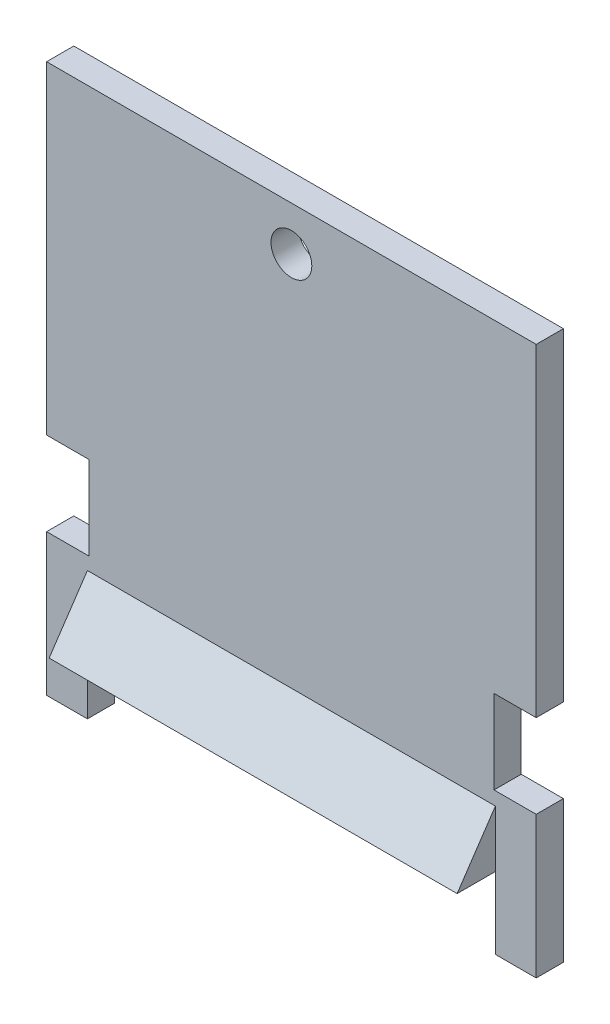
SolidWorks part; units mm, degrees
other "Camera1"
ref_plane "Front Plane" through (0, 0, 0) normal (0, 0, 1) x (1, 0, 0)
ref_plane "Top Plane" through (0, 0, 0) normal (0, 1, 0) x (1, 0, 0)
ref_plane "Right Plane" through (0, 0, 0) normal (1, 0, 0) x (0, 0, -1)
sketch "Sketch1" plane through (0, 0, 0) normal (1, 0, 0) x (0, 0, -1)
  line L0 (0, 0) -> (0, 40.35)
  line L1 (0, 40.35) -> (-2, 40.35)
  line L2 (-2, 40.35) -> (-2, 9.45)
  line L3 (-2, 9.45) -> (-6.5, 2.78)
  line L4 (-6.5, 2.78) -> (-2, 2.78)
  line L5 (-2, 2.78) -> (-2, 0)
  line L6 (-2, 0) -> (0, 0)
  dimension "D1" = 2
  dimension "D2" = 6.67
  dimension "D3" = 2.78
  dimension "D4" = 4.5
  dimension "D5" = 30.9
extrude "Boss-Extrude1" add sketch "Sketch1" along normal mid plane 36
sketch "Sketch2" plane through (0, 0, 0) normal (0, 0, -1) x (-1, 0, 0)
  line L0 (-18, 0) -> (18, 0) construction
  line L1 (-15, 0) -> (15, 0)
  line L2 (-15, 0) -> (-15, 2.78)
  line L3 (-15, 2.78) -> (15, 2.78)
  line L4 (15, 0) -> (15, 2.78)
  line L5 (-18, 2.78) -> (18, 2.78) construction
  line L6 (-18, 40.35) -> (18, 40.35) construction
  circle A0 centre (0, 37.1) radius 1.5
  point P6 (0, 2.78)
  dimension "D2" = 3
  dimension "D1" = 30
  dimension "D3" = 3.25
extrude "Cut-Extrude1" cut sketch "Sketch2" against normal through all
sketch "Sketch3" plane through (0, 0, 0) normal (0, 0, -1) x (-1, 0, 0)
  line L0 (-18, 0) -> (-18, 40.35) construction
  line L1 (-18, 16.575) -> (-14.9, 16.575)
  line L2 (-18, 16.575) -> (-18, 10.425)
  line L3 (-18, 10.425) -> (-14.9, 10.425)
  line L4 (-14.9, 16.575) -> (-14.9, 10.425)
  line L5 (18, 0) -> (18, 40.35) construction
  line L6 (18, 16.575) -> (14.9, 16.575)
  line L7 (18, 16.575) -> (18, 10.425)
  line L8 (18, 10.425) -> (14.9, 10.425)
  line L9 (14.9, 16.575) -> (14.9, 10.425)
  line L11 (-18, 0) -> (-15, 0) construction
  point P12 (-18, 13.5)
  dimension "D1" = 3.1
  dimension "D2" = 6.15
  dimension "D3" = 13.5
extrude "Cut-Extrude2" cut sketch "Sketch3" against normal through all
sketch "Sketch4" plane through (0, 0, 2) normal (0, 0, 1) x (1, 0, 0)
  line L0 (18, 2.78) -> (-18, 2.78) construction
  line L1 (-18, 10.425) -> (-15, 10.425)
  line L2 (-18, 10.425) -> (-18, 2.78)
  line L3 (-18, 2.78) -> (-15, 2.78)
  line L4 (-15, 10.425) -> (-15, 2.78)
  line L6 (18, 10.425) -> (15, 10.425)
  line L7 (18, 10.425) -> (18, 2.78)
  line L8 (18, 2.78) -> (15, 2.78)
  line L9 (15, 10.425) -> (15, 2.78)
  dimension "D1" = 30
extrude "Cut-Extrude3" cut sketch "Sketch4" along normal through all
sketch "Sketch5" plane through (-15, 0, 0) normal (-1, 0, 0) x (0, 0, 1)
  line L0 (0, 0) -> (0, 10.425) construction
  line L1 (6.5, 2.78) -> (0, 2.78)
  line L2 (6.5, 2.78) -> (6.5, 5.28)
  line L3 (6.5, 5.28) -> (0, 5.28)
  line L4 (0, 2.78) -> (0, 5.28)
  dimension "D1" = 2.5
extrude "Cut-Extrude4" cut sketch "Sketch5" against normal up to surface (30 mm away) up to face at (15, 5.0033, 3.5)
